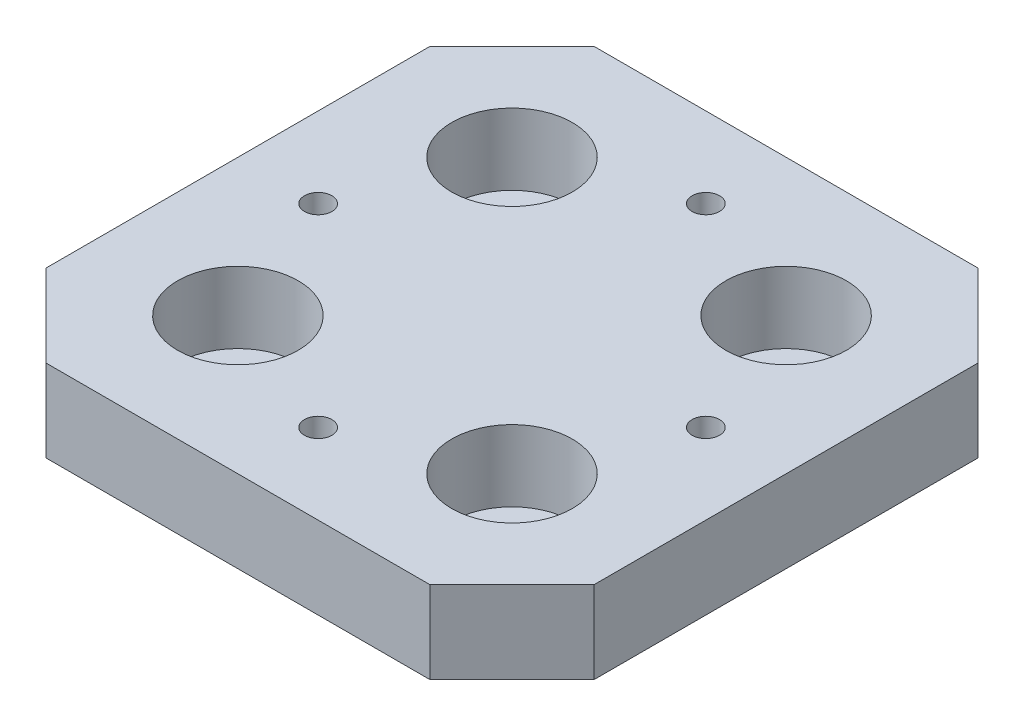
SolidWorks part; units mm, degrees
ref_plane "Front Plane" through (0, 0, 0) normal (0, 0, 1) x (1, 0, 0)
ref_plane "Top Plane" through (0, 0, 0) normal (0, 1, 0) x (1, 0, 0)
ref_plane "Right Plane" through (0, 0, 0) normal (1, 0, 0) x (0, 0, -1)
sketch "Sketch1" plane through (0, 0, 0) normal (0, 1, 0) x (1, 0, 0)
  line L1 (-25, -25) -> (25, -25)
  line L2 (-25, -25) -> (-25, 25)
  line L3 (-25, 25) -> (25, 25)
  line L4 (25, -25) -> (25, 25)
  line L5 (-25, -25) -> (25, 25) construction
  line L6 (-25, 25) -> (25, -25) construction
  point P0 (0, 0)
  dimension "D1" = 50
extrude "Boss-Extrude1" add sketch "Sketch1" along normal blind 7.5
hole_wizard "CBORE for M6 Hex Socket Head Cap Screw1" positions "Sketch2" profile "Sketch3" counterbore size "M6" standard "DIN" end condition up to next
sketch "Sketch2" plane through (0, 7.5, 0) normal (0, 1, 0) x (1, 0, 0)
  line L1 (-12.5, -12.5) -> (12.5, -12.5)
  line L2 (-12.5, -12.5) -> (-12.5, 12.5)
  line L3 (-12.5, 12.5) -> (12.5, 12.5)
  line L4 (12.5, -12.5) -> (12.5, 12.5)
  line L5 (-12.5, -12.5) -> (12.5, 12.5) construction
  line L6 (-12.5, 12.5) -> (12.5, -12.5) construction
  point P0 (-12.5, -12.5)
  point P2 (-12.5, 12.5)
  point P4 (12.5, 12.5)
  point P6 (12.5, -12.5)
  dimension "D1" = 25
sketch "Sketch3" plane through (-12.5, 7.5, 12.5) normal (1, 0, 0) x (0, 0, 1)
  line L0 (0, 0) -> (0, 7.5)
  line L1 (0, 7.5) -> (3.3, 7.5)
  line L3 (3.3, 7.5) -> (3.3, 6.5)
  line L4 (3.3, 6.5) -> (5.5, 6.5)
  line L5 (5.5, 6.5) -> (5.5, 0)
  line L7 (5.5, 0) -> (0, 0)
  line L11 (0, -6.35) -> (0, 107.95) construction
  dimension "Thru Hole Dia." = 6.6
  dimension "Thru Hole Depth" = 7.5
  dimension "C'Bore Dia." = 11
  dimension "C'Bore Depth" = 6.5
hole_wizard "M3 Tapped Hole1" positions "Sketch4" profile "Sketch5" tap size "M3" standard "DIN" end condition up to next
sketch "Sketch4" plane through (0, 7.5, 0) normal (0, 1, 0) x (1, 0, 0)
  line L1 (-17.6777, 0) -> (17.6777, 0) construction
  line L3 (0, 17.6777) -> (0, -17.6777) construction
  point P0 (0, 17.6777)
  point P2 (-17.6777, 0)
  point P4 (0, -17.6777)
  point P6 (17.6777, 0)
  dimension "D1" = 25
sketch "Sketch5" plane through (0, 7.5, -17.6777) normal (1, 0, 0) x (0, 0, 1)
  line L0 (0, 0) -> (0, 7.5)
  line L1 (0, 7.5) -> (1.25, 7.5)
  line L2 (1.25, 7.5) -> (1.25, 0)
  line L5 (1.25, 0) -> (0, 0)
  line L11 (0, -6.35) -> (0, 107.95) construction
  dimension "Thru Tap Drill Dia." = 2.5
  dimension "Thru Tap Drill Depth" = 7.5
cosmetic thread "Hole Thread1"
cosmetic thread "Hole Thread2"
cosmetic thread "Hole Thread3"
cosmetic thread "Hole Thread4"
chamfer "Chamfer1" distance 7.5 angle 45 4 edges at (-25, 3.75, -25) (25, 3.75, -25) (25, 3.75, 25) (-25, 3.75, 25)
